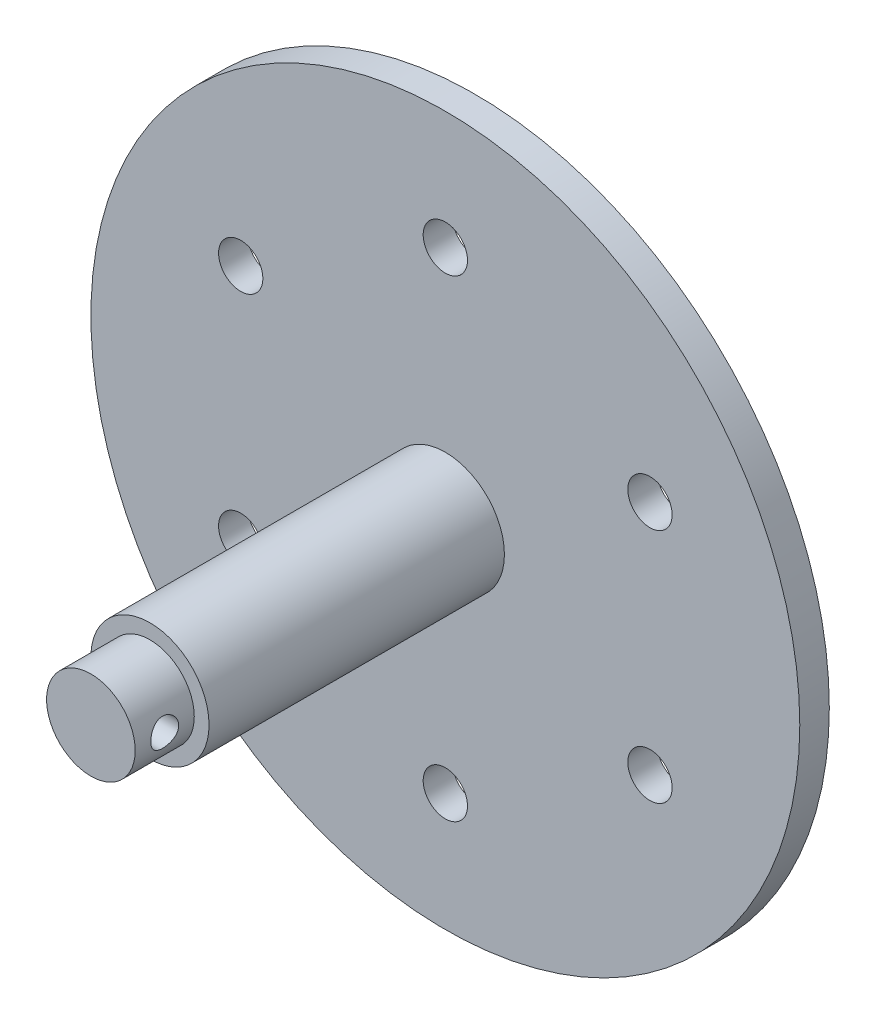
SolidWorks part; units mm, degrees
ref_plane "Front Plane" through (0, 0, 0) normal (0, 0, 1) x (1, 0, 0)
ref_plane "Top Plane" through (0, 0, 0) normal (0, 1, 0) x (1, 0, 0)
ref_plane "Right Plane" through (0, 0, 0) normal (1, 0, 0) x (0, 0, -1)
sketch "Sketch1" plane through (0, 0, 0) normal (0, 0, 1) x (1, 0, 0)
  circle A0 centre (0, 0) radius 50.8
  circle A1 centre (0, 0) radius 76.2
  circle A2 centre (0, 50.8) radius 4.7625
  circle A3 centre (43.9941, 25.4) radius 4.7625
  circle A4 centre (43.9941, -25.4) radius 4.7625
  circle A5 centre (0, -50.8) radius 4.7625
  circle A6 centre (-43.9941, -25.4) radius 4.7625
  circle A7 centre (-43.9941, 25.4) radius 4.7625
  point P18 (0, 0)
  dimension "D1" = 6
extrude "Boss-Extrude1" add sketch "Sketch1" along normal blind 6.35 contours A1 A7 A0 A2 A3 A4 A5 A6 | A7 A0 A6 A5 A4 A3 A2
sketch "Sketch2" plane through (0, 0, 6.35) normal (0, 0, 1) x (1, 0, 0)
  circle A0 centre (0, 0) radius 12.7
extrude "Boss-Extrude2" add sketch "Sketch2" along normal blind 76.2
sketch "Sketch3" plane through (0, 0, 82.55) normal (0, 0, 1) x (1, 0, 0)
  circle A0 centre (0, 0) radius 12.7
  circle A1 centre (0, 0) radius 9.525
extrude "Cut-Extrude1" cut sketch "Sketch3" against normal blind 12.7 contours A1 | A0
ref_plane "Plane1" through (9.525, 0, 0) normal (1, 0, 0) x (0, 0, -1)
sketch "Sketch4" plane through (9.525, 0, 0) normal (1, 0, 0) x (0, 0, -1)
  line L0 (-82.55, 0) -> (-76.2, 0) construction
  line L1 (-82.55, 9.525) -> (-82.55, -9.525) construction
  circle A0 centre (-76.2, 0) radius 3
extrude "Cut-Extrude2" cut sketch "Sketch4" against normal through all
